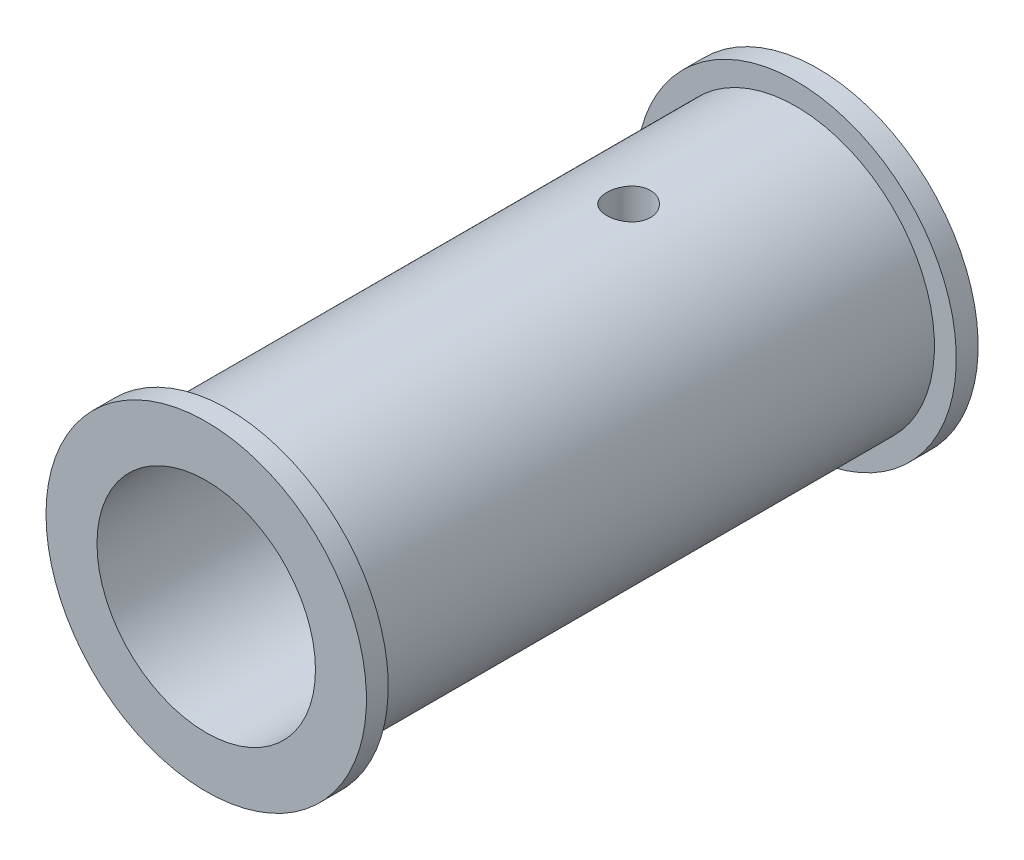
SolidWorks part; units mm, degrees
material "ABS"
ref_plane "Alzado" through (0, 0, 0) normal (0, 0, 1) x (1, 0, 0)
ref_plane "Planta" through (0, 0, 0) normal (0, 1, 0) x (1, 0, 0)
ref_plane "Vista lateral" through (0, 0, 0) normal (1, 0, 0) x (0, 0, -1)
sketch "Croquis1" plane through (0, 0, 0) normal (1, 0, 0) x (0, 0, -1)
  line L0 (0, 0) -> (-50000, 0) construction
  line L1 (-24, 7.5) -> (-24, 11)
  line L2 (-24, 7.5) -> (0, 7.5)
  line L3 (0, 7.5) -> (0, 0)
  line L4 (-24, 11) -> (-22.5, 11)
  line L5 (-22.5, 11) -> (-22.5, 9.5)
  line L6 (18, 8) -> (10, 8)
  line L7 (10, 8) -> (10, 0)
  line L8 (0, 0) -> (10, 0)
  line L9 (-22.5, 9.5) -> (16.5, 9.5)
  line L10 (16.5, 9.5) -> (16.5, 11)
  line L11 (16.5, 11) -> (18, 11)
  line L12 (18, 11) -> (18, 8)
  dimension "D1" = 16
  dimension "D2" = 1.5
  dimension "D3" = 1.5
  dimension "D4" = 1.5
  dimension "D5" = 42
  dimension "D6" = 8
  dimension "D7" = 2
  dimension "D8" = 10
revolve "Revolución1" add sketch "Croquis1" angle 360 about L0
sketch "Croquis2" plane through (0, 0, -10) normal (0, 0, -1) x (-1, 0, 0)
  line L0 (-1.1726, 1.125) -> (1.1726, 1.125)
  arc A0 (-1.1726, 1.125) -> (1.1726, 1.125) centre (0, 0) ccw
  dimension "D1" = 1.625
  dimension "D2" = 1.125
extrude "Cortar-Extruir1" cut sketch "Croquis2" against normal through all
sketch "Croquis3" plane through (0, 0, -10) normal (0, 0, -1) x (-1, 0, 0)
  line L0 (1.1726, 1.125) -> (-1.1726, 1.125) construction
  line L1 (-2.8, 4.625) -> (2.8, 4.625)
  line L2 (-2.8, 4.625) -> (-2.8, 2.125)
  line L3 (-2.8, 2.125) -> (2.8, 2.125)
  line L4 (2.8, 4.625) -> (2.8, 2.125)
  line L5 (-2.8, 4.625) -> (2.8, 2.125) construction
  line L6 (-2.8, 2.125) -> (2.8, 4.625) construction
  point P0 (0, 3.375)
  dimension "D1" = 2.5
  dimension "D2" = 5.6
  dimension "D3" = 1
extrude "Cortar-Extruir2" cut sketch "Croquis3" against normal through all
sketch "Croquis4" plane through (0, 0, 0) normal (0, 1, 0) x (1, 0, 0)
  line L0 (-1.625, 0) -> (1.625, 0) construction
  circle A0 centre (0, 5) radius 1.5
  dimension "D2" = 3
  dimension "D1" = 5
extrude "Cortar-Extruir3" cut sketch "Croquis4" along normal through all
